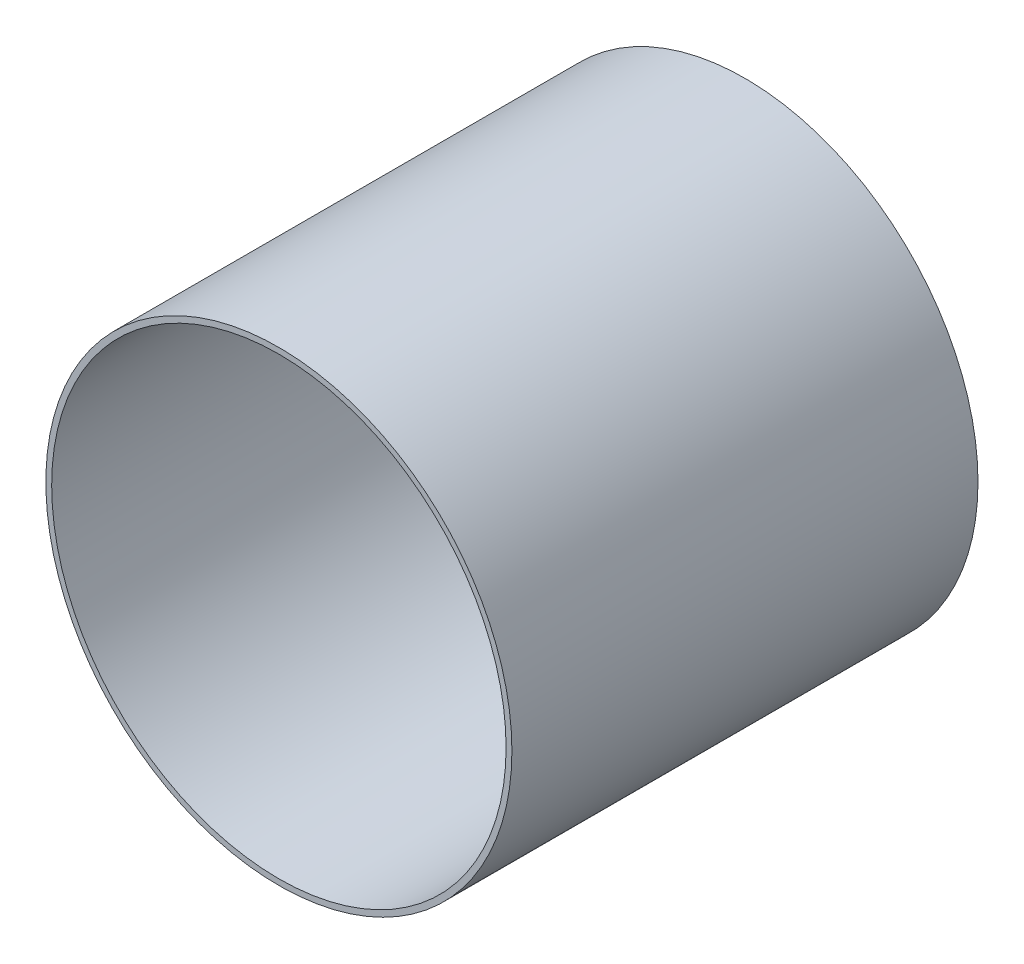
SolidWorks part; units mm, degrees
ref_plane "Plan de face" through (0, 0, 0) normal (0, 0, 1) x (1, 0, 0)
ref_plane "Plan de dessus" through (0, 0, 0) normal (0, 1, 0) x (1, 0, 0)
ref_plane "Plan de droite" through (0, 0, 0) normal (1, 0, 0) x (0, 0, -1)
sketch "Esquisse1" plane through (0, 0, 0) normal (0, 0, 1) x (1, 0, 0)
  circle A0 centre (0, 0) radius 20
  circle A1 centre (0, 0) radius 19.5
  dimension "D1" = 40
  dimension "D2" = 39
extrude "Boss.-Extru.1" add sketch "Esquisse1" along normal blind 40
